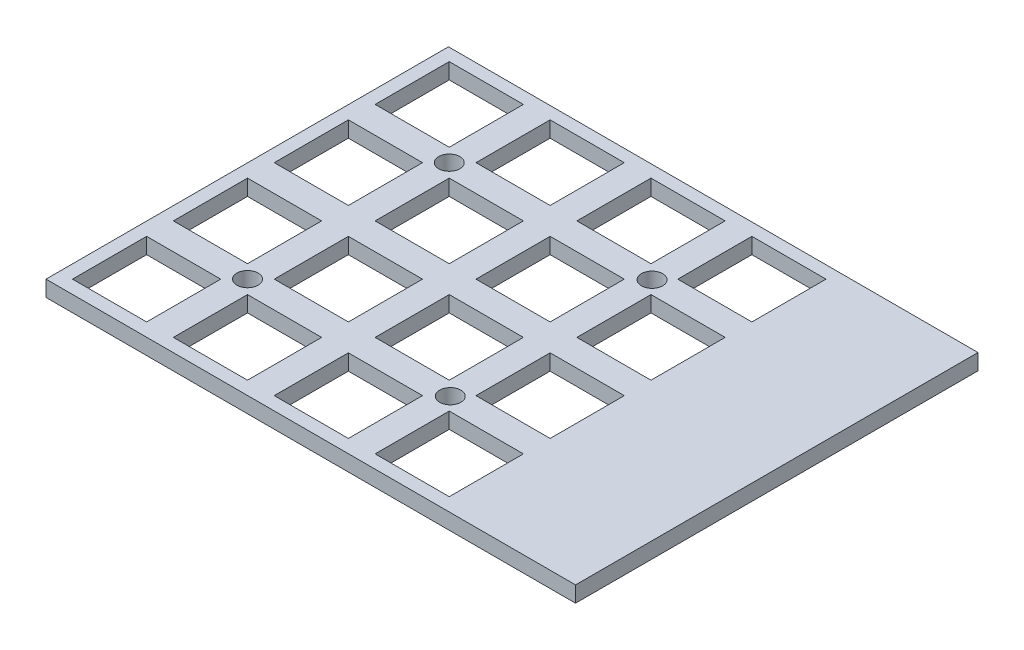
SolidWorks part; units mm, degrees
ref_plane "Front Plane" through (0, 0, 0) normal (0, 0, 1) x (1, 0, 0)
ref_plane "Top Plane" through (0, 0, 0) normal (0, 1, 0) x (1, 0, 0)
ref_plane "Right Plane" through (0, 0, 0) normal (1, 0, 0) x (0, 0, -1)
sketch "Sketch1" plane through (0, 0, 0) normal (0, 1, 0) x (1, 0, 0)
  line L1 (0, 0) -> (100, 0)
  line L2 (0, 0) -> (0, 76)
  line L3 (0, 76) -> (100, 76)
  line L4 (100, 0) -> (100, 76)
  dimension "D1" = 100
  dimension "D2" = 76
extrude "Boss-Extrude1" add sketch "Sketch1" along normal blind 3
fillet "Fillet1" [suppressed] radius 0.5
sketch "Sketch2" plane through (0, 3, 0) normal (0, 1, 0) x (1, 0, 0)
  line L0 (0, 0) -> (100, 0) construction
  line L1 (2.5, 2.5) -> (16.5, 2.5)
  line L2 (2.5, 2.5) -> (2.5, 16.5)
  line L3 (2.5, 16.5) -> (16.5, 16.5)
  line L4 (16.5, 2.5) -> (16.5, 16.5)
  line L5 (0, 76) -> (0, 0) construction
  dimension "D1" = 2.5
  dimension "D2" = 2.5
  dimension "D3" = 14
  dimension "D4" = 14
extrude "Cut-Extrude1" cut sketch "Sketch2" against normal through all both and the other way through all
pattern_linear "LPattern1" count 4 spacing 19.05 along (0, 0, -1) count 4 spacing 19.05 along (1, 0, 0) of "Cut-Extrude1"
sketch "Sketch4" plane through (0, 3, 0) normal (0, 1, 0) x (1, 0, 0)
  line L0 (35.55, 59.65) -> (21.55, 59.65) construction
  line L1 (16.5, 54.6) -> (16.5, 40.6) construction
  line L2 (54.6, 54.6) -> (54.6, 40.6) construction
  line L5 (35.55, 21.55) -> (21.55, 21.55) construction
  circle A0 centre (19.025, 57.125) radius 2
  circle A1 centre (57.3179, 57.125) radius 2
  circle A2 centre (19.025, 19.025) radius 2
  circle A3 centre (57.3179, 19.025) radius 2
  point P12 (0, 0)
  point P13 (0, 0)
  point P14 (0, 0)
  dimension "D3" = 4
  dimension "D5" = 2.525
  dimension "D1" = 2.525
  dimension "D2" = 2.525
  dimension "D4" = 2.7179
extrude "Cut-Extrude2" cut sketch "Sketch4" against normal through all both and the other way through all
